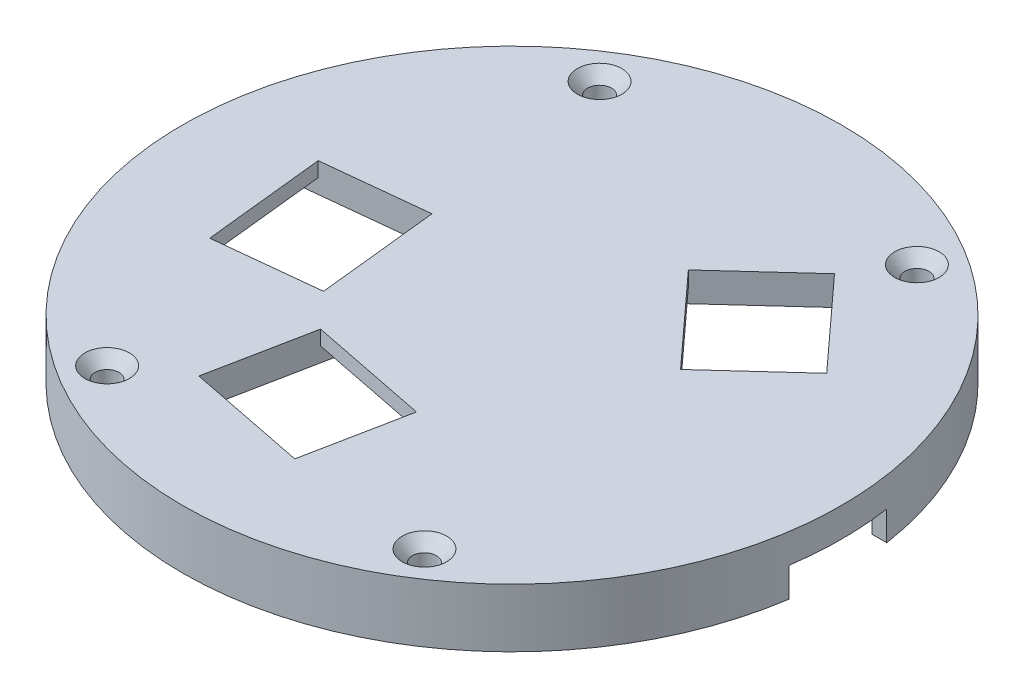
SolidWorks part; units mm, degrees
material "ABS"
ref_plane "Front Plane" through (0, 0, 0) normal (0, 0, 1) x (1, 0, 0)
ref_plane "Top Plane" through (0, 0, 0) normal (0, 1, 0) x (1, 0, 0)
ref_plane "Right Plane" through (0, 0, 0) normal (1, 0, 0) x (0, 0, -1)
sketch "Sketch2" plane through (0, 0, 0) normal (0, 1, 0) x (1, 0, 0)
  circle A0 centre (0, 0) radius 67.5
  dimension "D1" = 135
extrude "Palm base " add sketch "Sketch2" against normal blind 12 contours A0
shell "Bottom surface removed " thickness 6
sketch "Sketch3" plane through (0, 0, 0) normal (0, 1, 0) x (1, 0, 0)
  line L0 (-67.1227, -7.1271) -> (-13.1763, -66.2015) construction
  line L1 (-13.1763, -66.2015) -> (49.844, 45.5173) construction
  line L2 (49.844, 45.5173) -> (-67.1227, -7.1271) construction
  line L3 (0, 0) -> (49.844, 45.5173) construction
  line L4 (0, 0) -> (-13.1763, -66.2015) construction
  line L5 (0, 0) -> (-67.1227, -7.1271) construction
  line L6 (25.679, 40.3777) -> (42.5372, 21.9169)
  line L7 (7.3794, -26.9591) -> (-17.1396, -22.079)
  line L8 (-17.1396, -22.079) -> (-21.276, -42.8614)
  line L9 (42.5372, 21.9169) -> (26.8899, 7.6279)
  line L10 (26.8899, 7.6279) -> (10.0316, 26.0886)
  line L11 (10.0316, 26.0886) -> (25.679, 40.3777)
  line L12 (-21.276, -42.8614) -> (3.2431, -47.7415)
  line L13 (3.2431, -47.7415) -> (7.3794, -26.9591)
  line L14 (-26.1801, 9.7905) -> (-23.5404, -15.0698)
  line L15 (-23.5404, -15.0698) -> (-44.612, -17.3072)
  line L16 (-44.612, -17.3072) -> (-47.2516, 7.5531)
  line L17 (-47.2516, 7.5531) -> (-26.1801, 9.7905)
  line L18 (-4.8801, -24.5191) -> (-9.0165, -45.3014) construction
  line L19 (-24.8603, -2.6397) -> (-45.9318, -4.877) construction
  line L20 (0, 0) -> (0, 95.4963) construction
  circle A1 centre (0, 0) radius 67.5 construction
  point P0 (34.1081, 31.1473)
  dimension "D1" = 21.19
  dimension "D2" = 25
  dimension "D3" = 25
  dimension "D4" = 25
  dimension "D5" = 25
  dimension "D6" = 47.598
  dimension "D7" = 18.171
extrude "Through hole for finger base " cut sketch "Sketch3" against normal up to next
sketch "Sketch7" plane through (0, 0, 0) normal (0, 1, 0) x (1, 0, 0)
  line L1 (7.3794, -26.9591) -> (8.1798, -22.938)
  line L2 (8.1798, -22.938) -> (-16.3393, -18.0579)
  line L3 (-16.3393, -18.0579) -> (-17.1396, -22.079)
  line L4 (26.8899, 7.6279) -> (10.0316, 26.0886) construction
  line L5 (42.5372, 21.9169) -> (25.679, 40.3777)
  line L6 (26.8899, 7.6279) -> (10.0316, 26.0886)
  line L7 (26.8899, 7.6279) -> (10.0316, 26.0886)
  line L8 (7.3794, -26.9591) -> (-17.1396, -22.079)
  line L9 (-21.276, -42.8614) -> (-22.0763, -46.8825)
  line L10 (-22.0763, -46.8825) -> (2.4427, -51.7626)
  line L11 (7.0041, 23.3239) -> (23.8623, 4.8631)
  line L12 (23.8623, 4.8631) -> (26.8899, 7.6279)
  line L13 (25.679, 40.3777) -> (28.7065, 43.1424)
  line L14 (28.7065, 43.1424) -> (45.5648, 24.6817)
  line L15 (45.5648, 24.6817) -> (42.5372, 21.9169)
  line L16 (2.4427, -51.7626) -> (3.2431, -47.7415)
  line L17 (3.2431, -47.7415) -> (-21.276, -42.8614)
  line L18 (-23.5404, -15.0698) -> (-26.1801, 9.7905)
  line L19 (-26.1801, 9.7905) -> (-22.103, 10.2234)
  line L20 (-22.103, 10.2234) -> (-19.4633, -14.6369)
  line L21 (-19.4633, -14.6369) -> (-23.5404, -15.0698)
  line L23 (-47.2516, 7.5531) -> (-51.3287, 7.1202)
  line L24 (-51.3287, 7.1202) -> (-48.6891, -17.7401)
  line L25 (-48.6891, -17.7401) -> (-44.612, -17.3072)
  line L26 (-44.612, -17.3072) -> (-47.2516, 7.5531)
  line L27 (10.0316, 26.0886) -> (7.0041, 23.3239)
  line M2 (25.679, 40.3777) -> (42.5372, 21.9169)
  line M6 (26.8899, 7.6279) -> (10.0316, 26.0886)
  line M38 (-17.1396, -22.079) -> (7.3794, -26.9591)
  line M40 (3.2431, -47.7415) -> (-21.276, -42.8614)
  dimension "D1" = 4.1
  dimension "D2" = 4.1
  dimension "D3" = 4.1
extrude "Finger base cut offset from surface" cut sketch "Sketch7" against normal up to next from offset 3 contours L2 L3 L1 M38 | L10 L16 L9 M40 | L27 L11 L12 M6 | L15 L14 L13 M2 | L25 L26 L23 L24 | L18 L19 L20 L21 offset against normal yes
sketch "Sketch4" plane through (0, -12, 0) normal (0, -1, 0) x (1, 0, 0)
  circle A0 centre (0, 0) radius 64.5
  circle A1 centre (0, 0) radius 67.5
  circle A2 centre (0, 0) radius 67.5 construction
  dimension "D1" = 0
  dimension "D2" = 3
extrude "Side thickness cut " cut sketch "Sketch4" against normal up to surface (6 mm away) up to face at (26.2844, -6, -24.0028)
sketch "Reference sketch for holes" plane through (0, 0, 0) normal (0, 1, 0) x (1, 0, 0)
  line L0 (-32.5, 50.4356) -> (32.5, 50.4356) construction
  line L1 (32.5, 50.4356) -> (32.5, -50.4356) construction
  line L2 (32.5, -50.4356) -> (-32.5, -50.4356) construction
  line L3 (-32.5, -50.4356) -> (-32.5, 50.4356) construction
  line L4 (0, -50.4356) -> (0, 50.4356) construction
  line L5 (32.5, 0) -> (-32.5, 0) construction
  circle A1 centre (0, 0) radius 67.5 construction
  dimension "D1" = 7.5
  dimension "D2" = 35
hole_wizard "CSK for #8 Flat Head Socket Cap Screw1" positions "3DSketch1" profile "Sketch6" countersink size "#8" standard "ANSI Inch" end condition through all
sketch3d "3DSketch1"
  point P0 (-32.5, 0, -50.4356)
  point P3 (32.5, 0, -50.4356)
  point P6 (32.5, 0, 50.4356)
  point P9 (-32.5, 0, 50.4356)
sketch "Sketch6" plane through (-32.5, 0, -50.4356) normal (1, 0, 0) x (0, 0, 1)
  line L0 (0, 0) -> (0, 12)
  line L1 (0, 12) -> (2.4574, 12)
  line L2 (2.4574, 12) -> (2.4574, 2.4179)
  line L3 (2.4574, 2.4179) -> (4.5593, 0)
  line L5 (4.5593, 0) -> (0, 0)
  line L6 (-2.4574, 2.4179) -> (-4.5593, 0) construction
  line L11 (0, -6.35) -> (0, 107.95) construction
  dimension "Thru Hole Dia." = 4.9149
  dimension "Thru Hole Depth" = 12
  dimension "Near C'Sink Dia." = 9.1186
  dimension "Near C'Sink Angle" = 82
sketch "Sketch9" plane through (0, 0, 0) normal (1, 0, 0) x (0, 0, -1)
  line L0 (64.5, -6) -> (-21.3099, -6)
  line L1 (-51.2764, -6) -> (-64.5, -6)
  line L2 (-51.2764, -6) -> (-64.5, -6)
  line L3 (10, -6) -> (-10, -6)
  line L4 (-67.5, -12) -> (67.5, -12) construction
  line L5 (-67.5, -12) -> (67.5, -12) construction
  line L6 (10, -6) -> (10, -12)
  line L7 (-10, -6) -> (-10, -12)
  line L8 (-10, -12) -> (10, -12)
  line L9 (0, -12) -> (0, -6) construction
  dimension "D1" = 20
extrude "Slot for palm bottom" cut sketch "Sketch9" against normal up to surface and the other way up to surface contours L7 L8 L6 L3 up to face at (0, -12, 67.5) other way up to face at (0, -12, 67.5)
